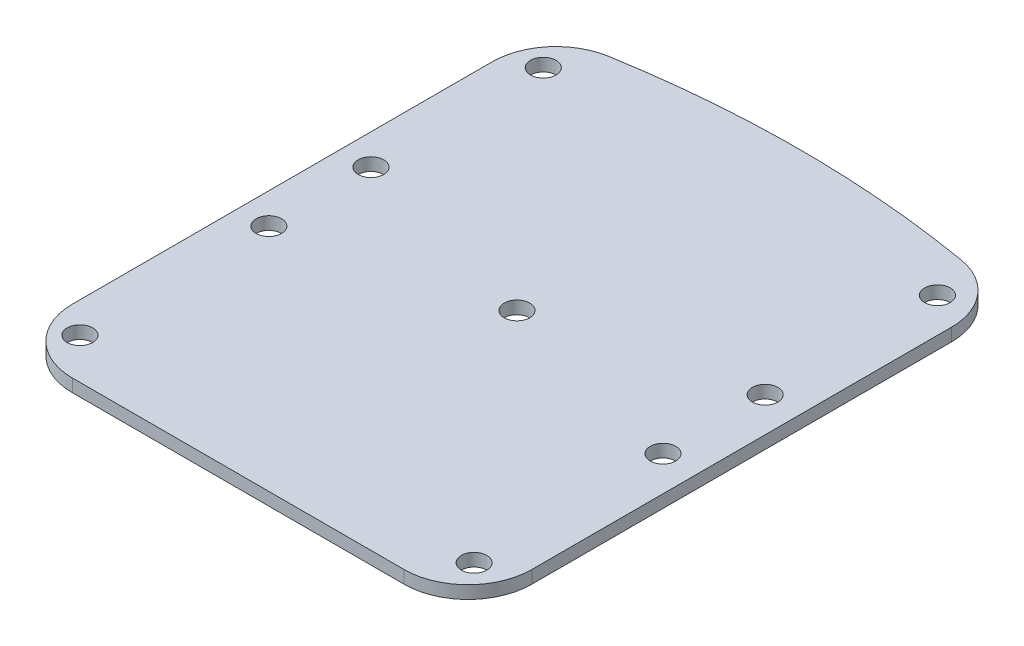
SolidWorks part; units mm, degrees
ref_plane "Front Plane" through (0, 0, 0) normal (0, 0, 1) x (1, 0, 0)
ref_plane "Top Plane" through (0, 0, 0) normal (0, 1, 0) x (1, 0, 0)
ref_plane "Right Plane" through (0, 0, 0) normal (1, 0, 0) x (0, 0, -1)
sketch "Sketch1" plane through (0, 0, 0) normal (0, 1, 0) x (1, 0, 0)
  line L1 (-64.2024, -110) -> (65.7976, -110)
  line L5 (-89.2024, -35) -> (-89.2024, -85)
  line L6 (90.7976, -35) -> (90.7976, -85)
  line L7 (-89.2024, 79.4733) -> (-89.2024, 31.4733)
  line L20 (90.7976, 31.4733) -> (90.7976, 79.4617)
  line L30 (-89.2024, -35) -> (-89.2024, 31.4733)
  line L31 (90.7976, -35) -> (90.7976, 31.4733)
  arc A0 (-68.4209, 104.1148) -> (70.0206, 104.1024) centre (0.7637, -300.0058) cw
  arc A1 (65.7976, -110) -> (90.7976, -85) centre (65.7976, -85) ccw
  arc A2 (-64.2024, -110) -> (-89.2024, -85) centre (-64.2024, -85) cw
  arc A3 (90.7976, 79.4617) -> (70.0206, 104.1024) centre (65.7976, 79.4617) ccw
  arc A4 (-89.2024, 79.4733) -> (-68.4209, 104.1148) centre (-64.2024, 79.4733) cw
  point P0 (0, 0)
  point P25 (-0.7976, 109.9942)
  dimension "D3" = 25
  dimension "D4" = 25
extrude "Boss-Extrude1" add sketch "Sketch1" along normal blind 5
sketch "Sketch5" plane through (0, 5, 0) normal (0, 1, 0) x (1, 0, 0)
  line L1 (-89.2024, -85) -> (-89.2024, 79.4733) construction
  circle A0 centre (-77.2024, 20) radius 5
  circle A1 centre (-77.2024, -20) radius 5
  circle A2 centre (-77.2024, 87.5) radius 5
  circle A3 centre (-77.2024, -94) radius 5
  circle A4 centre (0, 0) radius 5
  circle A5 centre (77.2024, -94) radius 5
  circle A6 centre (77.2024, -20) radius 5
  circle A7 centre (77.2024, 20) radius 5
  circle A8 centre (77.2024, 87.5) radius 5
  dimension "D2" = 12
  dimension "D6" = 67.5
  dimension "D8" = 10
  dimension "D5" = 12
extrude "Cut-Extrude2" cut sketch "Sketch5" against normal blind 10
